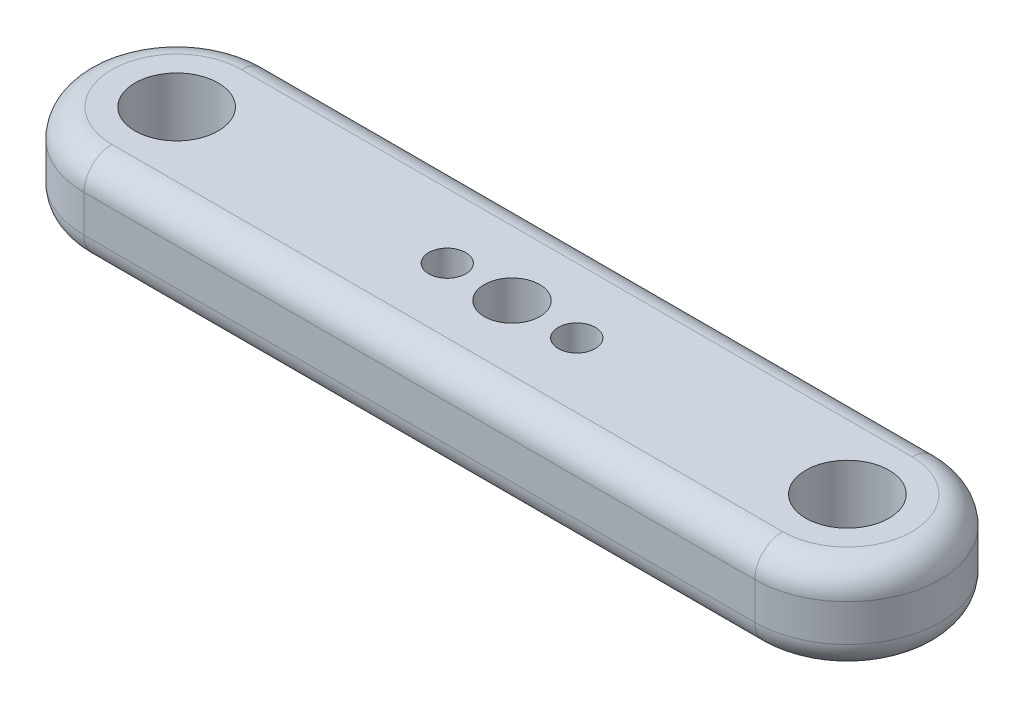
SolidWorks part; units mm, degrees
ref_plane "Front Plane" through (0, 0, 0) normal (0, 0, 1) x (1, 0, 0)
ref_plane "Top Plane" through (0, 0, 0) normal (0, 1, 0) x (1, 0, 0)
ref_plane "Right Plane" through (0, 0, 0) normal (1, 0, 0) x (0, 0, -1)
sketch "Sketch2" plane through (0, 0, 0) normal (0, 1, 0) x (1, 0, 0)
  line L4 (-36.25, 10) -> (36.25, 10)
  line L10 (36.25, -10) -> (-36.25, -10)
  arc A1 (0, -5) -> (0, 5) centre (0, 0) ccw
  circle A5 centre (0, 0) radius 5
  circle A6 centre (-36.25, 0) radius 5
  circle A7 centre (36.25, 0) radius 5
  arc A8 (-36.25, 10) -> (-36.25, -10) centre (-36.25, 0) ccw
  arc A9 (36.25, -10) -> (36.25, 10) centre (36.25, 0) ccw
  circle A10 centre (-36.25, 0) radius 10 construction
  circle A11 centre (36.25, 0) radius 10 construction
  point P3 (-19.375, 0)
  dimension "D1" = 5
  dimension "D2" = 5
extrude "Boss-Extrude1" add sketch "Sketch2" along normal blind 10 contours L10 A9 L4 A8 A5 A1 A6 A7
fillet "Fillet1" radius 3 8 edges at (-46.25, 0, 0) (0, 0, 10) (46.25, 0, 0) (-46.25, 10, 0) (0, 10, 10) (46.25, 10, 0) (0, 0, -10) (0, 10, -10)
sketch "Sketch3" plane through (0, 10, 0) normal (0, 1, 0) x (1, 0, 0)
  line L0 (0, 0) -> (-6.5, 0)
  line L1 (-6.5, 0) -> (7.6495, 0)
  circle A0 centre (0, 0) radius 5
  circle M5 centre (0, 0) radius 5
extrude "Boss-Extrude2" add sketch "Sketch3" against normal blind 10 contours L0 L1 M5 | L1 L0 M5
sketch "Sketch4" plane through (0, 10, 0) normal (0, 1, 0) x (1, 0, 0)
  line L0 (0, 0) -> (-8.2, 0)
  line L1 (0, 0) -> (8.2, 0)
  circle A0 centre (-8.2, 0) radius 1.5
  circle A1 centre (8.2, 0) radius 1.5
sketch "Sketch5" plane through (0, 10, 0) normal (0, 1, 0) x (1, 0, 0)
  circle A0 centre (-36.25, 0) radius 4.5
  circle A1 centre (-36.25, 0) radius 5
  circle A2 centre (36.25, 0) radius 5
  circle A3 centre (36.25, 0) radius 4.5
extrude "Boss-Extrude3" add sketch "Sketch5" against normal up to surface (10 mm away) up to face at (0, 0, 0)
sketch "Sketch6" plane through (0, 10, 0) normal (0, 1, 0) x (1, 0, 0)
  line L0 (7, 0) -> (-7, 0)
  circle A1 centre (-7, 0) radius 2
  circle A2 centre (7, 0) radius 2
extrude "Cut-Extrude1" cut sketch "Sketch6" against normal blind 10
sketch "Sketch7" plane through (0, 10, 0) normal (0, 1, 0) x (1, 0, 0)
  circle A0 centre (0, 0) radius 3
extrude "Cut-Extrude2" cut sketch "Sketch7" against normal blind 10
